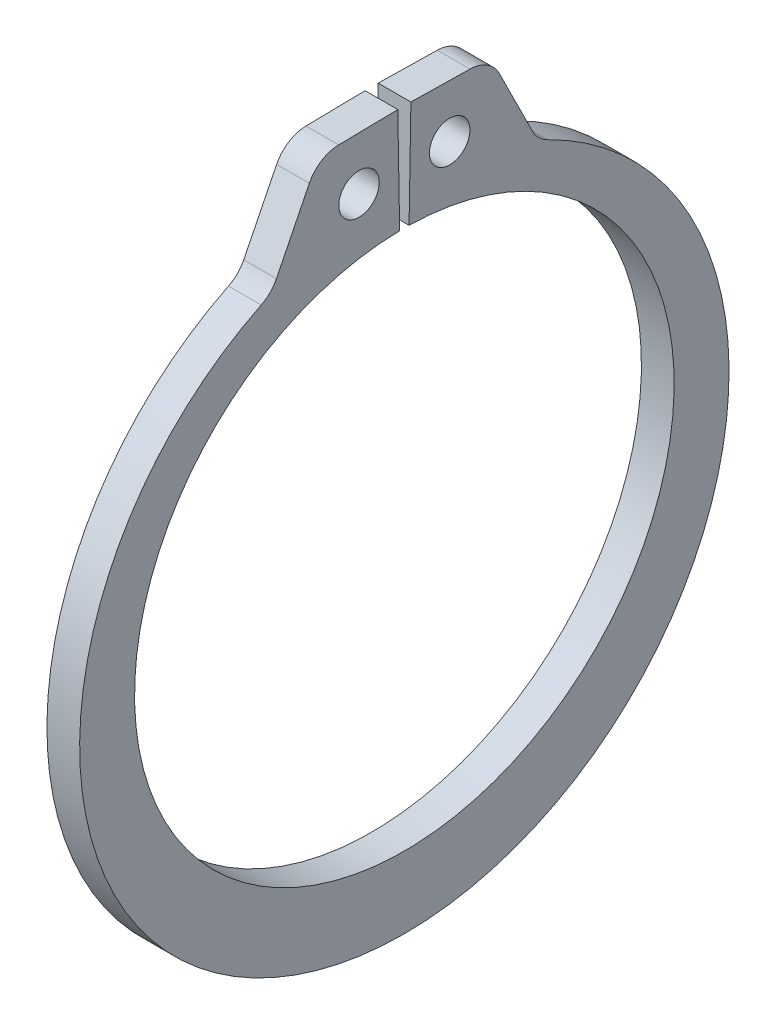
SolidWorks part; units mm, degrees
material "Cast Carbon Steel"
ref_plane "Front" through (0, 0, 0) normal (0, 0, 1) x (1, 0, 0)
ref_plane "Top" through (0, 0, 0) normal (0, 1, 0) x (1, 0, 0)
ref_plane "Right" through (0, 0, 0) normal (1, 0, 0) x (0, 0, -1)
sketch "Sketch1" plane through (0, 0, 0) normal (1, 0, 0) x (0, 0, -1)
  line L0 (0, 0) -> (0, 8.8011) construction
  line L1 (-0.1536, 8.7998) -> (-0.2139, 12.2536)
  line L2 (0.2139, 12.2536) -> (2.8043, 12.2084)
  line L3 (2.8043, 12.2084) -> (4.342, 9.1152)
  line L4 (0.1536, 8.7998) -> (0.2139, 12.2536)
  line L5 (-0.2139, 12.2536) -> (-2.8043, 12.2084)
  line L6 (-2.8043, 12.2084) -> (-4.342, 9.1152)
  line L7 (-4.342, 9.1152) -> (-3.7849, 7.9457) construction
  line L8 (4.342, 9.1152) -> (3.7849, 7.9457) construction
  line L9 (0, -8.8011) -> (0, -11.1379) construction
  line L10 (-2.8043, 12.2084) -> (-0.1536, 8.7998) construction
  line L11 (0, 8.8011) -> (0, 12.2555) construction
  line L12 (-8.8011, 0) -> (8.8011, 0) construction
  circle A0 centre (0, 0) radius 8.8011 construction
  arc A1 (-0.1536, 8.7998) -> (0.1536, 8.7998) centre (0, 0) ccw
  circle A3 centre (0, 0) radius 13.589 construction
  circle A4 centre (-1.4789, 10.5041) radius 0.6604
  circle A5 centre (1.4789, 10.5041) radius 0.6604
  arc A6 (-4.342, 9.1152) -> (4.342, 9.1152) centre (0, -0.5459) ccw
  point P0 (0, -11.1379)
  dimension "A" = 17.6022
  dimension "D2" = 2.5908
  dimension "L" = 27.178
  dimension "Hole" = 1.3208
  dimension "Smin" = 1.2954
  dimension "Smax" = 2.3368
  dimension "H" = 3.4544
  dimension "Angle" = 1
extrude "Extrude1" add sketch "Sketch1" along normal mid plane 1.0668
fillet "Fillet1" radius 1.0922 4 edges at (0, 9.1152, 4.342) (0, 9.1152, -4.342) (0, 12.2084, 2.8043) (0, 12.2084, -2.8043)
sketch "Sketch2" plane through (0, 0, 0) normal (0, 0, 1) x (1, 0, 0)
  line L0 (-5.9182, 0) -> (15.4178, 0)
  line L1 (15.4178, 0) -> (15.4178, -9.525)
  line L2 (-0.5842, -9.525) -> (-5.334, -9.525)
  line L3 (15.4178, -9.525) -> (0.5842, -9.525)
  line L4 (0.5842, -9.525) -> (0.5842, -8.9408)
  line L5 (0.5842, -8.9408) -> (-0.5842, -8.9408)
  line L6 (-0.5842, -8.9408) -> (-0.5842, -9.525)
  line L7 (-0.5842, -9.525) -> (-5.9182, -9.525) construction
  line L8 (-5.9182, -9.525) -> (-5.9182, 0) construction
  line L9 (15.4178, 0) -> (76.391, 0) construction
  line L10 (-5.334, -9.525) -> (-5.9182, -8.9408)
  line L11 (-5.9182, -8.9408) -> (-5.9182, 0)
  point P10 (0, -8.9408)
  dimension "D1" = 45
  dimension "Dg" = 17.8816
  dimension "Ds" = 19.05
  dimension "W" = 1.1684
  dimension "D2" = 21.336
  dimension "D3" = 5.334
revolve "Revolve1" [suppressed] add sketch "Sketch2" angle 360 about L9
delete or keep bodies "Body-Delete1" [suppressed] type delete bodies bodies 122
equation "\"D2@Sketch2\" = \"D1@Extrude1\"*20"
equation "\"D3@Sketch2\" = \"D2@Sketch2\"/4"
equation "\"D2@Sketch1\" = \"H@Sketch1\"*.75"
